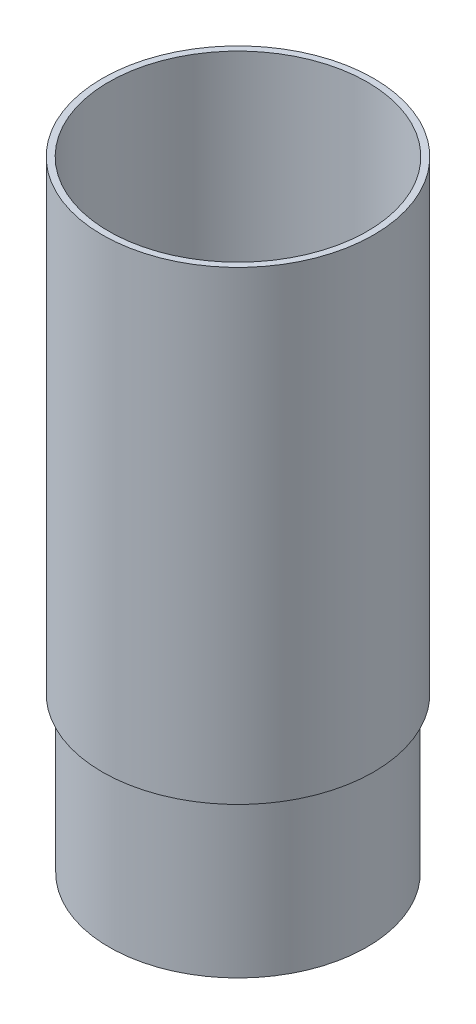
SolidWorks part; units mm, degrees
ref_plane "Front Plane" through (0, 0, 0) normal (0, 0, 1) x (1, 0, 0)
ref_plane "Top Plane" through (0, 0, 0) normal (0, 1, 0) x (1, 0, 0)
ref_plane "Right Plane" through (0, 0, 0) normal (1, 0, 0) x (0, 0, -1)
sketch "Sketch1" plane through (0, 0, 0) normal (0, 0, 1) x (1, 0, 0)
  line L0 (0, 0) -> (0, 54.0332) construction
  line L1 (-20.0787, -6.8588) -> (-20.0787, 20.445)
  line L2 (-20.0787, 20.445) -> (-21.1836, 24.5685)
  line L3 (-21.1836, 24.5685) -> (-21.1836, 94.7412)
  line L4 (-21.1836, 94.7412) -> (-22.225, 94.7412)
  line L5 (-22.225, 94.7412) -> (-22.225, 18.5412)
  line L6 (-22.225, 18.5412) -> (-21.1201, 18.5412)
  line L7 (-21.1201, 18.5412) -> (-21.1201, -6.8588)
  line L8 (-21.1201, -6.8588) -> (-20.0787, -6.8588)
  dimension "D1" = 42.2402
  dimension "D2" = 44.45
  dimension "D3" = 25.4
  dimension "D4" = 101.6
  dimension "D5" = 1.0414
  dimension "D6" = 1.0414
  dimension "D7" = 15
revolve "Revolve1" add sketch "Sketch1" angle 360 about L0
